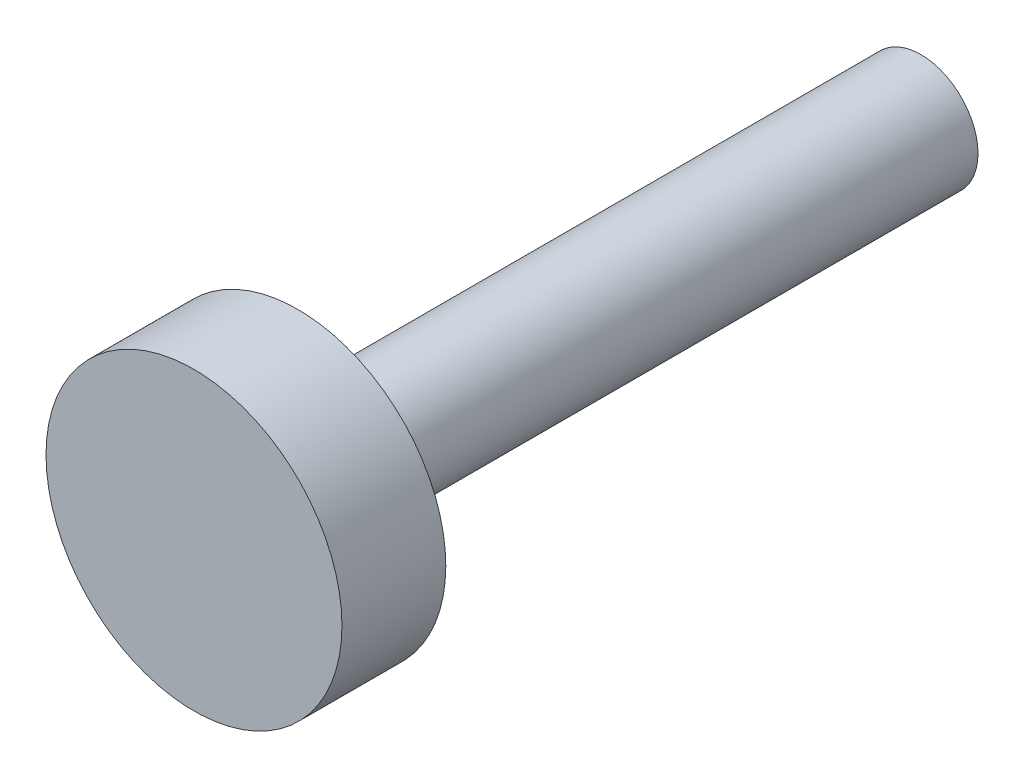
SolidWorks part; units mm, degrees
ref_plane "Ebene vorne" through (0, 0, 0) normal (0, 0, 1) x (1, 0, 0)
ref_plane "Ebene oben" through (0, 0, 0) normal (0, 1, 0) x (1, 0, 0)
ref_plane "Ebene rechts" through (0, 0, 0) normal (1, 0, 0) x (0, 0, -1)
sketch "Skizze1" plane through (0, 0, 0) normal (1, 0, 0) x (0, 0, -1)
  line L0 (0, 0) -> (14, 0)
  line L1 (14, 0) -> (14, 1.1)
  line L2 (14, 1.1) -> (2, 1.1)
  line L3 (2, 1.1) -> (2, 2.85)
  line L4 (2, 2.85) -> (0, 2.85)
  line L5 (0, 2.85) -> (0, 0)
  dimension "D1" = 12
  dimension "D2" = 1.1
  dimension "D3" = 2.85
  dimension "D4" = 2
revolve "Rotation1" add sketch "Skizze1" angle 360 about L0
